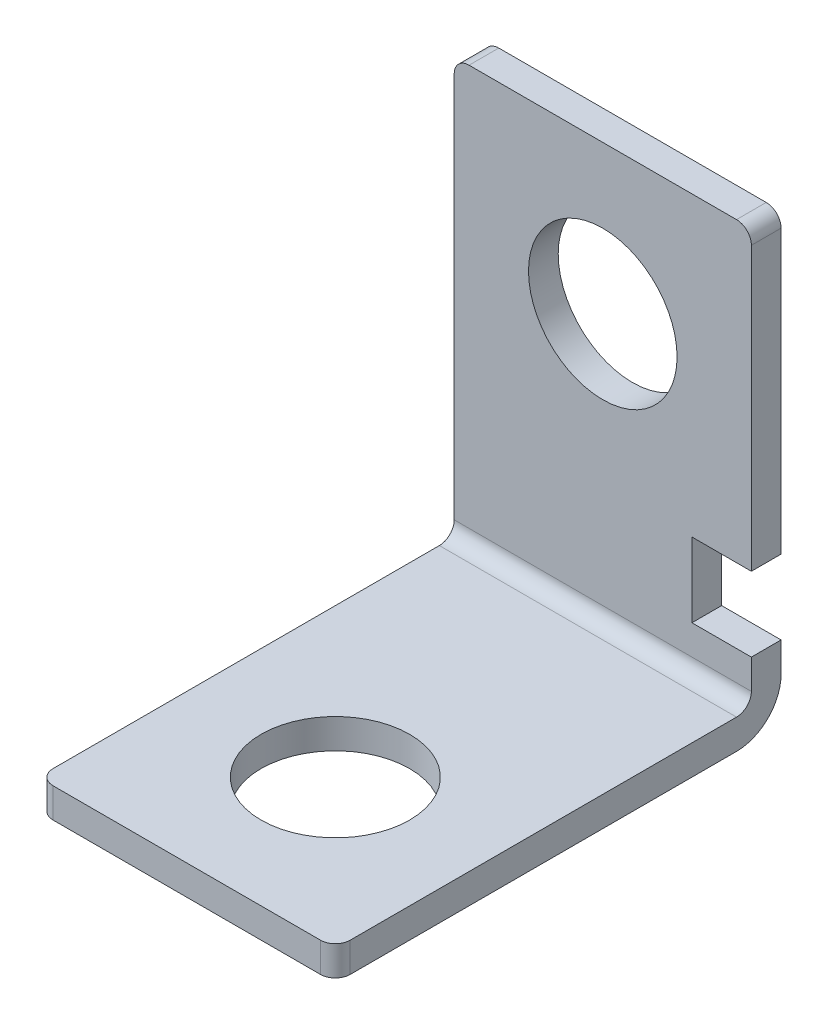
SolidWorks part; units mm, degrees
material "6061 Alloy"
ref_plane "Front Plane" through (0, 0, 0) normal (0, 0, 1) x (1, 0, 0)
ref_plane "Top Plane" through (0, 0, 0) normal (0, 1, 0) x (1, 0, 0)
ref_plane "Right Plane" through (0, 0, 0) normal (1, 0, 0) x (0, 0, -1)
sketch "Sketch1" plane through (0, 0, 0) normal (1, 0, 0) x (0, 0, -1)
  line L0 (-30, 0) -> (0, 0)
  line L1 (0, 0) -> (0, 30)
  dimension "D1" = 30
  dimension "D2" = 30
extrude "Extrude-Thin1" add sketch "Sketch1" along normal mid plane 20 thin thin type one direction reverse wall 2
sketch "Sketch2" plane through (0, 0, 2) normal (0, 0, 1) x (1, 0, 0)
  line L0 (10, 2) -> (10, 30) construction
  line L1 (10, 10) -> (6, 10)
  line L2 (10, 10) -> (10, 5)
  line L3 (10, 5) -> (6, 5)
  line L4 (6, 10) -> (6, 5)
  line L5 (10, 30) -> (-10, 30) construction
  dimension "D1" = 5
  dimension "D2" = 4
  dimension "D3" = 20
extrude "Cut-Extrude1" cut sketch "Sketch2" against normal blind 10 contours L4 L3 L2 L1
fillet "Fillet1" radius 3 1 edges at (0, 0, 0)
fillet "Fillet2" radius 1 1 edges at (0, 2, 2)
sketch "Sketch3" plane through (0, 0, 2) normal (0, 0, 1) x (1, 0, 0)
  line L0 (10, 30) -> (-10, 30) construction
  line L1 (-10, 3) -> (-10, 30) construction
  circle A0 centre (0, 20) radius 5
  point P2 (0, 30)
  dimension "D1" = 10
  dimension "D2" = 10
  dimension "D3" = 10
extrude "Cut-Extrude2" cut sketch "Sketch3" against normal blind 10
sketch "Sketch4" plane through (0, 2, 0) normal (0, 1, 0) x (1, 0, 0)
  line L0 (10, -30) -> (-10, -30) construction
  line L2 (10, -30) -> (10, -3) construction
  circle A0 centre (0, -20) radius 5
  dimension "D1" = 10
  dimension "D2" = 10
  dimension "D3" = 10
extrude "Cut-Extrude3" cut sketch "Sketch4" against normal blind 10
fillet "Fillet3" radius 1 4 edges at (-10, 1, 30) (10, 1, 30) (-10, 30, 1) (10, 30, 1)
